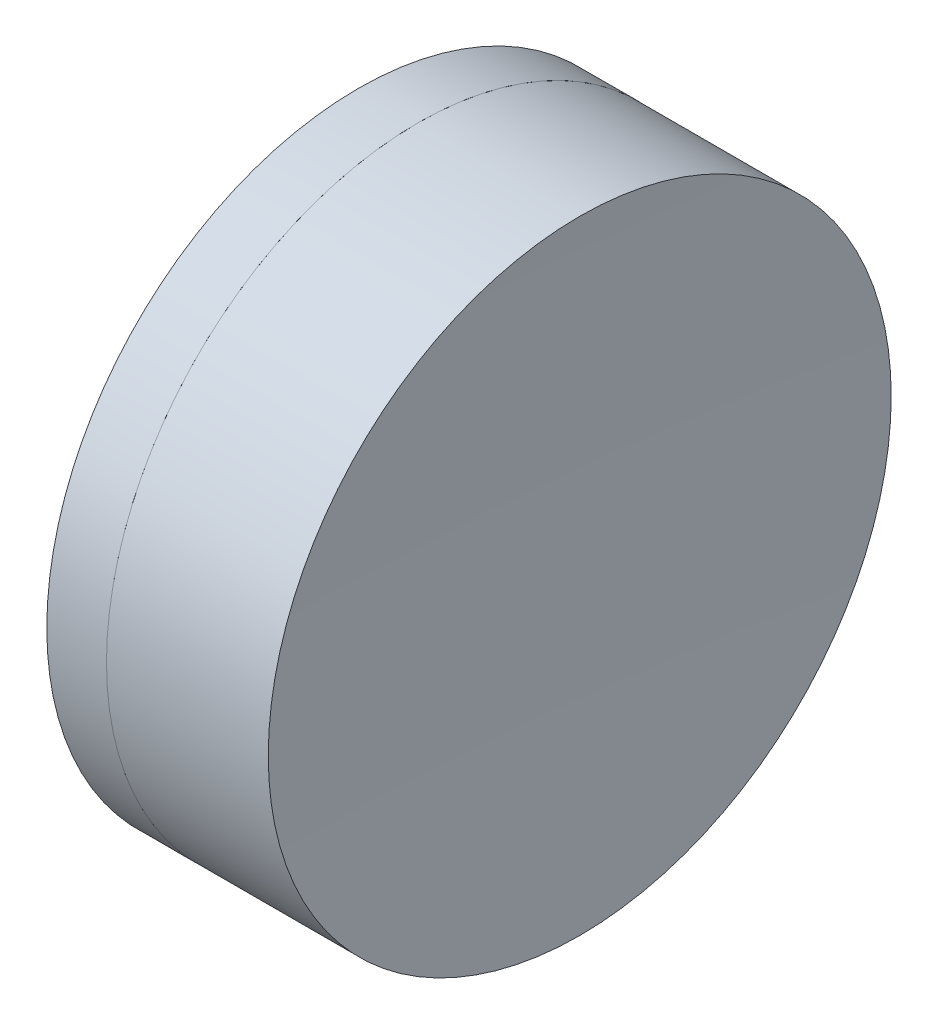
SolidWorks part; units mm, degrees
ref_plane "前视基准面" through (0, 0, 0) normal (0, 0, 1) x (1, 0, 0)
ref_plane "上视基准面" through (0, 0, 0) normal (0, 1, 0) x (1, 0, 0)
ref_plane "右视基准面" through (0, 0, 0) normal (1, 0, 0) x (0, 0, -1)
sketch "草图1" plane through (0, 0, 0) normal (0, 1, 0) x (1, 0, 0)
  line L0 (-0.8161, 0) -> (26.6816, 0) construction
  line L1 (22.3437, -6.35) -> (23.5607, -6.35)
  line L2 (22.3437, 6.35) -> (23.5607, 6.35)
  arc A0 (23.5607, -6.35) -> (23.5607, 6.35) centre (12.2859, 0) ccw
  arc A1 (22.3437, 6.35) -> (22.3437, -6.35) centre (32.5259, 0) ccw
  point P10 (20.5259, 0)
  point P11 (25.2259, 0)
  dimension "D3" = 12
  dimension "D4" = 12.94
  dimension "D1" = 6.35
  dimension "D2" = 6.35
  dimension "D5" = 4.7
revolve "旋转1" add sketch "草图1" angle 360 about L0
sketch "草图2" plane through (0, 0, 0) normal (0, 1, 0) x (1, 0, 0)
  line L0 (-0.5519, 0) -> (35.3831, 0) construction
  line L2 (23.5607, 6.35) -> (26.8589, 6.35)
  line L3 (23.5607, -6.35) -> (26.8589, -6.35)
  arc A0 (26.8589, 6.35) -> (26.8589, -6.35) centre (178.4359, 0) ccw
  arc A1 (23.5607, -6.35) -> (23.5607, 6.35) centre (12.2859, 0) ccw construction
  arc A2 (23.5607, -6.35) -> (23.5607, 6.35) centre (12.2859, 0) ccw
  point P4 (25.2259, 0)
  point P8 (26.7259, 0)
  point P9 (35.3831, 0)
  point P11 (104.2871, 0)
  dimension "D1" = 151.71
  dimension "D2" = 1.5
revolve "旋转2" add sketch "草图2" angle 360 about L0
